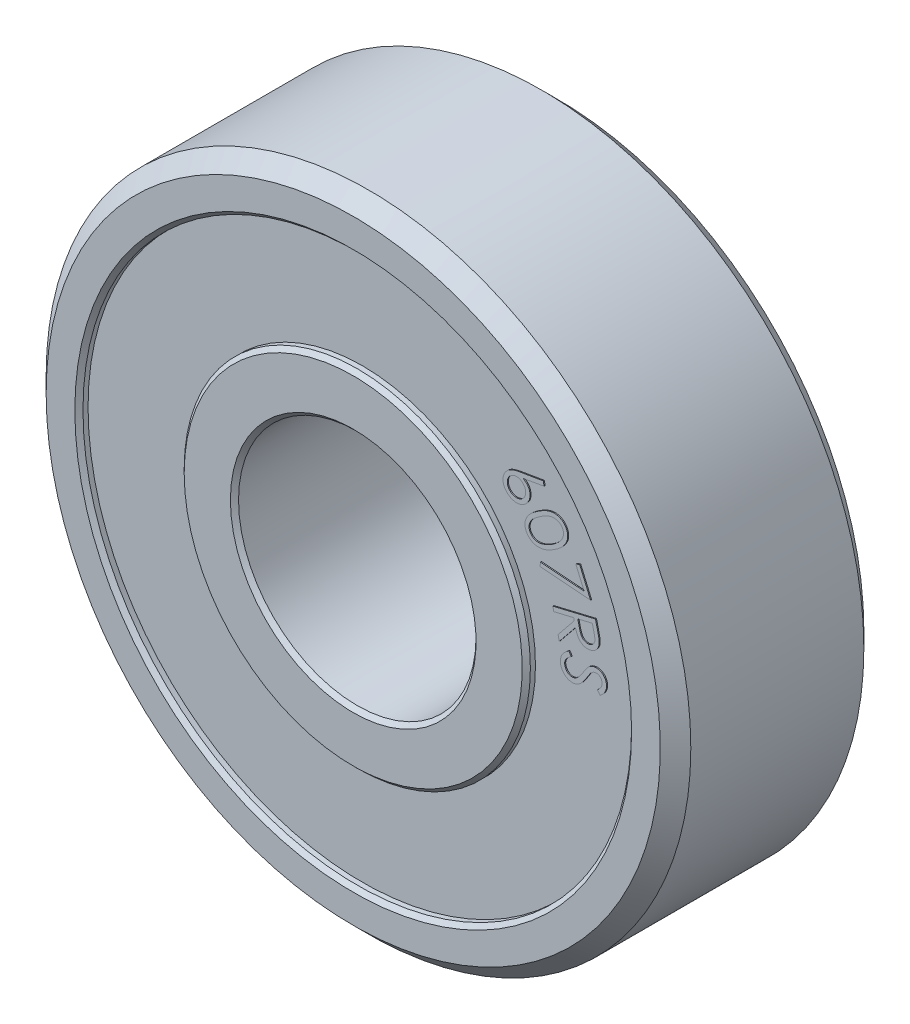
SolidWorks part; units mm, degrees
ref_plane "Front Plane" through (0, 0, 0) normal (0, 0, 1) x (1, 0, 0)
ref_plane "Top Plane" through (0, 0, 0) normal (0, 1, 0) x (1, 0, 0)
ref_plane "Right Plane" through (0, 0, 0) normal (1, 0, 0) x (0, 0, -1)
sketch "Sketch3" plane through (0, 0, 0) normal (0, 1, 0) x (1, 0, 0)
  line L0 (0, 0) -> (-9.5, 0) construction
  line L1 (0, 0) -> (0, 3) construction
  line L2 (0, 3) -> (-9.5, 3) construction
  line L3 (-9.5, 3) -> (-9.5, 0) construction
  line L4 (-3.5, 3) -> (-3.5, -3)
  line L5 (-3.5, 3) -> (-5.1015, 3)
  line L6 (-9.5, -3) -> (-9.5, 3)
  line L7 (-9.5, 3) -> (-8.0845, 3)
  line L8 (-8.0845, 3) -> (-8.0845, 2.73)
  line L9 (-8.0845, 2.73) -> (-5.1015, 2.73)
  line L10 (-5.1015, 2.73) -> (-5.1015, 3)
  line L11 (-3.5, -3) -> (-5.1015, -3)
  line L12 (-5.1015, -2.73) -> (-5.1015, -3)
  line L13 (-8.0845, -2.73) -> (-5.1015, -2.73)
  line L14 (-8.0845, -3) -> (-8.0845, -2.73)
  line L15 (-9.5, -3) -> (-8.0845, -3)
  point P12 (-3.5, 0)
  dimension "D1" = 9.5
  dimension "D2" = 3
  dimension "D3" = 3.5
  dimension "D4" = 5.1015
  dimension "D5" = 8.0845
  dimension "D6" = 0.27
revolve "Revolve1" add sketch "Sketch3" angle 360 about L1
chamfer "Chamfer1" distance 0.45 angle 45 2 edges at (9.5, 0, -3) (9.5, 0, 3)
chamfer "Chamfer2" distance 0.12 angle 45 6 edges at (5.1015, 0, 3) (3.5, 0, 3) (3.5, 0, -3) (5.1015, 0, -3) (8.0845, 0, 3) (8.0845, 0, -3)
sketch "Sketch4" plane through (0, 0, 2.73) normal (0, 0, 1) x (1, 0, 0)
  circle A0 centre (0, 0) radius 5.9375 construction
  text T0 "607RS" font "Century Gothic" height 1.3
  dimension "D1" = 11.875
extrude "Boss-Extrude1" add sketch "Sketch4" along normal blind 0.03
sketch "Sketch5" plane through (0, 0, -2.73) normal (0, 0, -1) x (-1, 0, 0)
  circle A0 centre (0, 0) radius 5.9375 construction
  text T0 "607RS" font "Century Gothic" height 1.3
  dimension "D1" = 11.875
extrude "Boss-Extrude2" add sketch "Sketch5" along normal blind 0.03
equation "\"InnerDiameter\"= 7mm"
equation "\"OuterDiameter\"= 19mm"
equation "\"Width\"= 6mm"
equation "\"D1@Sketch3\"= 0.5 * \"OuterDiameter\""
equation "\"D2@Sketch3\"= 0.5 * \"Width\""
equation "\"D3@Sketch3\"=0.5 * \"InnerDiameter\""
equation "\"D4@Sketch3\"= (\"OuterDiameter\" * 0.537 )/2"
equation "\"D5@Sketch3\"= (\"OuterDiameter\" *  0.851)/2"
equation "\"D6@Sketch3\"=\"Width\" * 0.045"
equation "\"D1@Chamfer1\"=\"Width\" * 0.075"
equation "\"D1@Chamfer2\"=\"Width\"*0.02"
equation "\"D1@Sketch4\"=\"OuterDiameter\"*0.625"
equation "\"D1@Boss-Extrude1\"=\"Width\"* 0.005"
equation "\"D1@Sketch5\"=\"OuterDiameter\" *0.625"
equation "\"D1@Boss-Extrude2\"=\"Width\"*0.005"
